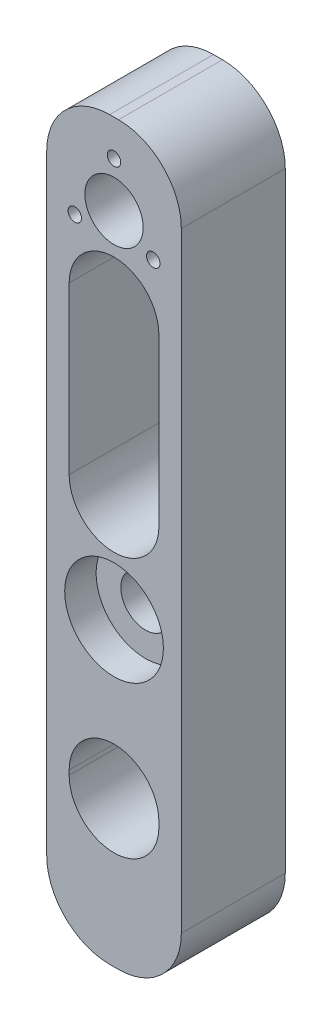
SolidWorks part; units mm, degrees
ref_plane "Front Plane" through (0, 0, 0) normal (0, 0, 1) x (1, 0, 0)
ref_plane "Top Plane" through (0, 0, 0) normal (0, 1, 0) x (1, 0, 0)
ref_plane "Right Plane" through (0, 0, 0) normal (1, 0, 0) x (0, 0, -1)
sketch "Sketch1" plane through (0, 0, 0) normal (0, 0, 1) x (1, 0, 0)
  line L0 (-15, -17) -> (0, 0) construction
  line L1 (-15, 67) -> (15, 67)
  line L2 (-15, 67) -> (-15, -17)
  line L3 (-15, -17) -> (15, -17)
  line L4 (15, 67) -> (15, -17)
  line L5 (0, 0) -> (15, -17) construction
  line L6 (-15, 67) -> (0, 50) construction
  line L7 (0, 50) -> (15, 67) construction
  circle A0 centre (0, 0) radius 7.9823
  circle A1 centre (0, 50) radius 11
  dimension "D3" = 30
  dimension "D4" = 22
  dimension "D5" = 15.9646
  dimension "D1" = 50
  dimension "D2" = 17
extrude "Boss-Extrude1" add sketch "Sketch1" along normal blind 23.1638
sketch "Sketch2" plane through (0, 0, 23.1638) normal (0, 0, 1) x (1, 0, 0)
  circle A0 centre (0, 0) radius 4
  circle A1 centre (0, 0) radius 7.9823 construction
  circle A2 centre (0, 0) radius 7.9823
  dimension "D1" = 8
extrude "Boss-Extrude2" add sketch "Sketch2" against normal up to surface (23.1638 mm away) up to face at (0, 25, 0)
sketch "Sketch3" plane through (0, 0, 23.1638) normal (0, 0, 1) x (1, 0, 0)
  circle A0 centre (0, 0) radius 4
extrude "Boss-Extrude3" add sketch "Sketch3" against normal blind 32.1638
sketch "Sketch4" plane through (0, 0, 0) normal (0, 0, -1) x (-1, 0, 0)
  circle A0 centre (0, 50) radius 11 construction
  circle A1 centre (0, 50) radius 11
  circle A2 centre (0, 50) radius 5.5
  dimension "D1" = 5.5
extrude "Boss-Extrude4" add sketch "Sketch4" against normal blind 16.1638
fillet "Fillet1" radius 14 2 edges at (-15, -17, 11.5819) (15, -17, 11.5819)
sketch "Sketch5" plane through (0, 0, 23.1638) normal (0, 0, 1) x (1, 0, 0)
  line L0 (15, -3) -> (15, 67) construction
  line L1 (-15, 67) -> (15, 67)
  line L2 (-15, 67) -> (-15, 147)
  line L3 (-15, 147) -> (15, 147)
  line L4 (15, 67) -> (15, 147)
  dimension "D1" = 80
extrude "Boss-Extrude5" add sketch "Sketch5" against normal up to surface (23.1638 mm away) up to face at (0, 14.7002, 0)
sketch "Sketch6" plane through (0, 0, 23.1638) normal (0, 0, 1) x (1, 0, 0)
  line L0 (-8.75, 123.8446) -> (8.75, 123.8446) construction
  line L1 (8.75, 123.8446) -> (0, 139) construction
  line L2 (0, 139) -> (-8.75, 123.8446) construction
  line L3 (15, 147) -> (-15, 147) construction
  line L4 (-8.75, 123.8446) -> (0, 128.8964) construction
  line L5 (0, 128.8964) -> (0, 139) construction
  line L6 (8.75, 123.8446) -> (0, 128.8964) construction
  circle A0 centre (-8.75, 123.8446) radius 1.5
  circle A1 centre (8.75, 123.8446) radius 1.5
  circle A2 centre (0, 139) radius 1.5
  circle A3 centre (0, 128.8964) radius 6.5
  point P7 (0, 50)
  dimension "D1" = 3
  dimension "D4" = 13
  dimension "D2" = 8
  dimension "D3" = 17.5
extrude "Cut-Extrude1" cut sketch "Sketch6" against normal through all
sketch "Sketch7" plane through (0, 0, 23.1638) normal (0, 0, 1) x (1, 0, 0)
  line L0 (15, 147) -> (-15, 147) construction
  line L2 (-10, 110) -> (-10, 73)
  line L3 (10, 110) -> (10, 73)
  line L4 (-10, 16) -> (-10, 15)
  line L5 (10, 16) -> (10, 15)
  arc A0 (10, 110) -> (-10, 110) centre (0, 110) ccw
  arc A1 (-10, 73) -> (10, 73) centre (0, 73) ccw
  arc A2 (10, 16) -> (-10, 16) centre (0, 16) ccw
  arc A3 (-10, 15) -> (10, 15) centre (0, 15) ccw
  point P1 (0, 0)
  point P3 (0, 50)
  dimension "D1" = 20
  dimension "D2" = 37
  dimension "D3" = 37
  dimension "D4" = 15
  dimension "D5" = 1
extrude "Cut-Extrude2" cut sketch "Sketch7" against normal up to surface (23.1638 mm away) up to face at (-7.25, 123.8446, 0)
fillet "Fillet2" radius 14 2 edges at (15, 147, 11.5819) (-15, 147, 11.5819)
